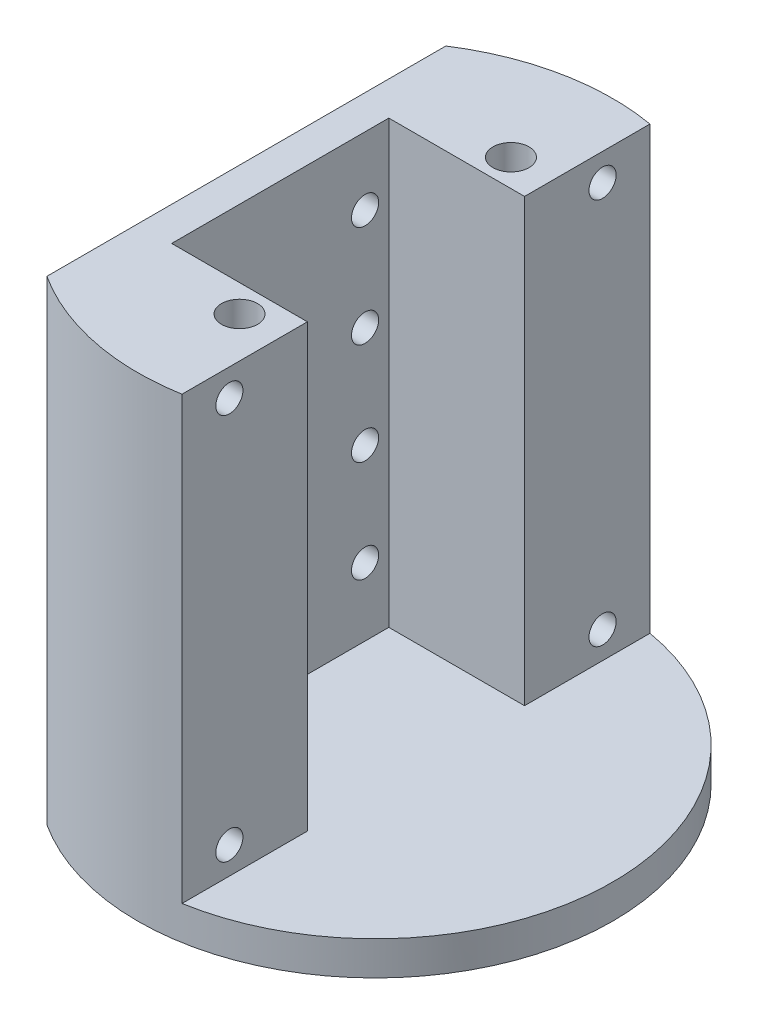
SolidWorks part; units mm, degrees
ref_plane "Front Plane" through (0, 0, 0) normal (0, 0, 1) x (1, 0, 0)
ref_plane "Top Plane" through (0, 0, 0) normal (0, 1, 0) x (1, 0, 0)
ref_plane "Right Plane" through (0, 0, 0) normal (1, 0, 0) x (0, 0, -1)
sketch "Sketch1" plane through (0, 0, 0) normal (0, 1, 0) x (1, 0, 0)
  line L0 (33.02, 20.32) -> (39.5335, 20.32)
  line L1 (33.02, -20.32) -> (-17.78, -20.32)
  line L2 (33.02, -20.32) -> (33.02, 20.32)
  line L3 (33.02, 20.32) -> (-17.78, 20.32)
  line L4 (-17.78, -20.32) -> (-17.78, 20.32)
  line L5 (33.02, -20.32) -> (-17.78, 20.32) construction
  line L6 (33.02, 20.32) -> (-17.78, -20.32) construction
  line L7 (33.02, -20.32) -> (39.5335, -20.32)
  line L8 (7.62, 20.32) -> (7.62, 43.792)
  line L9 (7.62, -20.32) -> (7.62, -43.792)
  line L10 (-24.13, 37.3302) -> (-24.13, -37.3302)
  circle A0 centre (0, 0) radius 44.45
  point P3 (7.62, 0)
  dimension "D1" = 88.9
  dimension "D2" = 50.8
  dimension "D3" = 40.64
  dimension "D4" = 7.62
  dimension "D5" = 6.35
extrude "Boss-Extrude1" add sketch "Sketch1" along normal blind 88.9 contours L8 A0 L9 L1 L4 L3
sketch "Sketch2" plane through (-17.78, 0, 0) normal (1, 0, 0) x (0, 0, -1)
  line L0 (-15.875, 76.2) -> (15.875, 76.2) construction
  line L1 (0, 76.2) -> (0, 0) construction
  line L2 (-20.32, 0) -> (20.32, 0) construction
  line L3 (-20.32, 88.9) -> (20.32, 88.9) construction
  circle A0 centre (-15.875, 76.2) radius 2.54
  circle A1 centre (15.875, 76.2) radius 2.54
  circle A2 centre (-15.875, 57.15) radius 2.54
  circle A3 centre (15.875, 57.15) radius 2.54
  circle A4 centre (-15.875, 38.1) radius 2.54
  circle A5 centre (15.875, 38.1) radius 2.54
  circle A6 centre (-15.875, 19.05) radius 2.54
  circle A7 centre (15.875, 19.05) radius 2.54
  dimension "D3" = 5.08
  dimension "D5" = 19.05
  dimension "D1" = 31.75
  dimension "D2" = 12.7
  dimension "D4" = 4
extrude "Cut-Extrude1" cut sketch "Sketch2" against normal blind 4.445
sketch "Sketch5" plane through (0, 88.9, 0) normal (0, 1, 0) x (1, 0, 0)
  line L0 (0, 25.4) -> (0, -25.4) construction
  circle A0 centre (0, 25.4) radius 3.175
  circle A1 centre (0, -25.4) radius 3.175
  point P0 (0, 25.4)
  point P1 (0, -25.4)
  point P2 (0, 0)
  point P12 (0, 25.4)
  point P14 (0, -25.4)
  dimension "D2" = 6.35
  dimension "D3" = 6.35
  dimension "D1" = 50.8
hole_wizard "1/4 Clearance Hole1" positions "Sketch5" profile "Sketch6" hole size "1/4" standard "ANSI Inch" end condition through all
sketch "Sketch6" plane through (0, 88.9, 25.4) normal (1, 0, 0) x (0, 0, 1)
  line L0 (0, 0) -> (0, 88.9)
  line L1 (0, 88.9) -> (3.3782, 88.9)
  line L2 (3.3782, 88.9) -> (3.3782, 0)
  line L5 (3.3782, 0) -> (0, 0)
  line L11 (0, -6.35) -> (0, 107.95) construction
  dimension "Thru Hole Dia." = 6.7564
  dimension "Thru Hole Depth" = 88.9
sketch "Sketch7" plane through (0, 0, 0) normal (0, -1, 0) x (1, 0, 0)
  line L2 (7.62, -20.32) -> (7.62, -43.792) construction
  line L3 (7.62, -20.32) -> (-17.78, -20.32) construction
  line L4 (7.62, 20.32) -> (7.62, 43.792) construction
  line L5 (-17.78, 20.32) -> (-17.78, -20.32) construction
  line L6 (7.62, 20.32) -> (-17.78, 20.32) construction
  line L7 (7.62, -20.32) -> (7.62, -43.792)
  line L8 (7.62, -20.32) -> (-17.78, -20.32)
  line L9 (7.62, 20.32) -> (7.62, 43.792)
  line L10 (-17.78, 20.32) -> (-17.78, -20.32)
  line L11 (7.62, 20.32) -> (-17.78, 20.32)
  arc A0 (7.62, -43.792) -> (7.62, 43.792) centre (0, 0) ccw
extrude "Boss-Extrude3" add sketch "Sketch7" against normal blind 6.35
sketch "Sketch8" plane through (7.62, 0, 0) normal (1, 0, 0) x (0, 0, -1)
  line L0 (-20.32, 6.35) -> (20.32, 6.35) construction
  line L1 (-34.925, 11.43) -> (34.925, 11.43) construction
  line L2 (-34.925, 11.43) -> (-34.925, 83.82) construction
  line L3 (-34.925, 83.82) -> (34.925, 83.82) construction
  line L4 (34.925, 11.43) -> (34.925, 83.82) construction
  line L5 (-34.925, 11.43) -> (34.925, 83.82) construction
  line L6 (-34.925, 83.82) -> (34.925, 11.43) construction
  line L7 (20.32, 88.9) -> (43.792, 88.9) construction
  circle A0 centre (-34.925, 83.82) radius 2.54
  circle A1 centre (34.925, 83.82) radius 2.54
  circle A2 centre (-34.925, 11.43) radius 2.54
  circle A3 centre (34.925, 11.43) radius 2.54
  point P0 (0, 47.625)
  dimension "D4" = 5.08
  dimension "D1" = 69.85
  dimension "D2" = 5.08
  dimension "D3" = 5.08
extrude "Cut-Extrude2" cut sketch "Sketch8" against normal blind 4.445
